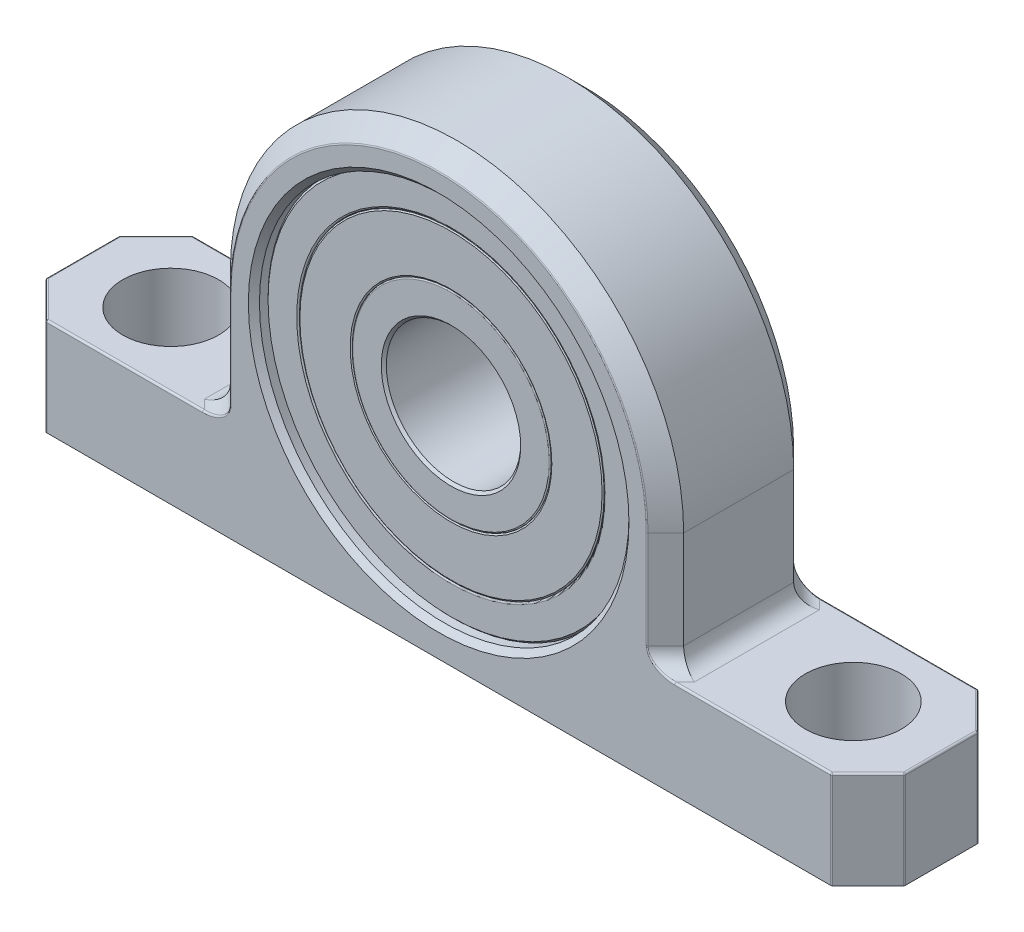
SolidWorks part; units mm, degrees
ref_plane "Front Plane" through (0, 0, 0) normal (0, 0, 1) x (1, 0, 0)
ref_plane "Top Plane" through (0, 0, 0) normal (0, 1, 0) x (1, 0, 0)
ref_plane "Right Plane" through (0, 0, 0) normal (1, 0, 0) x (0, 0, -1)
sketch "Sketch1" plane through (0, 0, 0) normal (0, 0, 1) x (1, 0, 0)
  line L0 (33.7344, 0) -> (33.7344, -17.272)
  line L1 (33.7344, -17.272) -> (63.8969, -17.272)
  line L2 (63.8969, -17.272) -> (63.8969, -31.75)
  line L3 (63.8969, -31.75) -> (-63.8969, -31.75)
  line L4 (-63.8969, -31.75) -> (-63.8969, -17.272)
  line L5 (-63.8969, -17.272) -> (-33.7344, -17.272)
  line L6 (-33.7344, -17.272) -> (-33.7344, 0)
  circle A0 centre (0, 0) radius 10
  arc A1 (33.7344, 0) -> (-33.7344, 0) centre (0, 0) ccw
  circle A2 centre (0, 0) radius 27.5
  point P12 (0, 27.5)
  point P13 (0, 10)
  dimension "ID" = 20
  dimension "Bearing OD" = 55
  dimension "Block OD" = 67.4688
  dimension "Collar Height" = 14.478
  dimension "Overall Length" = 127.7937
  dimension "Center Height" = 31.75
  dimension "Overall Height" = 65.4844
sketch "Sketch2" plane through (0, 0, 0) normal (0, 1, 0) x (1, 0, 0)
  line L0 (0, 10.9141) -> (0, -10.9141) construction
  line L1 (-50.8, 0) -> (50.8, 0) construction
  circle A0 centre (50.8, 0) radius 7.1437 construction
  circle A1 centre (-50.8, 0) radius 7.1437 construction
  dimension "Mounting Hole Diameter" = 14.2875
  dimension "Overall Width" = 21.8281
  dimension "Mounting Hole Center -to-Center" = 101.6
sketch "Sketch3" plane through (0, 0, 0) normal (0, 0, 1) x (1, 0, 0)
  line L0 (33.7344, 0) -> (33.7344, -17.272) construction
  line L1 (63.8969, -17.272) -> (63.8969, -31.75) construction
  line L2 (33.7344, -17.272) -> (63.8969, -17.272) construction
  line L3 (63.8969, -31.75) -> (-63.8969, -31.75) construction
  line L4 (-63.8969, -31.75) -> (-63.8969, -17.272) construction
  line L5 (-63.8969, -17.272) -> (-33.7344, -17.272) construction
  line L6 (-33.7344, -17.272) -> (-33.7344, 0) construction
  line L7 (33.7344, 0) -> (33.7344, -17.272)
  line L8 (63.8969, -17.272) -> (63.8969, -31.75)
  line L9 (33.7344, -17.272) -> (63.8969, -17.272)
  line L10 (63.8969, -31.75) -> (-63.8969, -31.75)
  line L11 (-63.8969, -31.75) -> (-63.8969, -17.272)
  line L12 (-63.8969, -17.272) -> (-33.7344, -17.272)
  line L13 (-33.7344, -17.272) -> (-33.7344, 0)
  arc A0 (33.7344, 0) -> (-33.7344, 0) centre (0, 0) ccw construction
  circle A1 centre (0, 0) radius 27.5 construction
  arc A2 (33.7344, 0) -> (-33.7344, 0) centre (0, 0) ccw
  circle A3 centre (0, 0) radius 27.5
extrude "Extrude1" add sketch "Sketch3" along normal up to vertex (10.9141 mm away) and the other way up to vertex (10.9141 mm away) up to point (0, 0, 10.9141) other way up to point (0, 0, -10.9141)
sketch "Sketch4" plane through (0, -17.272, 0) normal (0, 1, 0) x (1, 0, 0)
  line L0 (-63.8969, 10.9141) -> (-63.8969, 5.457)
  line L1 (-63.8969, -10.9141) -> (-63.8969, 10.9141) construction
  line L2 (-63.8969, 5.457) -> (-58.4398, 10.9141)
  line L3 (-33.7344, 10.9141) -> (-63.8969, 10.9141) construction
  line L4 (-58.4398, 10.9141) -> (-63.8969, 10.9141)
  line L5 (0, 0) -> (0, 10.9141) construction
  line L6 (0, 0) -> (-50.8, 0) construction
  line L7 (58.4398, 10.9141) -> (63.8969, 10.9141)
  line L8 (63.8969, 5.457) -> (58.4398, 10.9141)
  line L9 (63.8969, 10.9141) -> (63.8969, 5.457)
  line L10 (63.8969, -10.9141) -> (63.8969, -5.457)
  line L11 (63.8969, -5.457) -> (58.4398, -10.9141)
  line L12 (58.4398, -10.9141) -> (63.8969, -10.9141)
  line L13 (-58.4398, -10.9141) -> (-63.8969, -10.9141)
  line L14 (-63.8969, -5.457) -> (-58.4398, -10.9141)
  line L15 (-63.8969, -10.9141) -> (-63.8969, -5.457)
  circle A0 centre (-50.8, 0) radius 7.1437 construction
  circle A1 centre (50.8, 0) radius 7.1437 construction
  circle A2 centre (-50.8, 0) radius 7.1437
  circle A3 centre (50.8, 0) radius 7.1437
  dimension "D1" = 45
  dimension "D2" = 5.457
extrude "Cut-Extrude1" cut sketch "Sketch4" against normal through all
chamfer "Chamfer3" distance 2.7285 angle 45 6 edges at (-33.7344, -8.636, -10.9141) (0, 33.7344, -10.9141) (33.7344, -8.636, -10.9141) (-33.7344, -8.636, 10.9141) (0, 33.7344, 10.9141) (33.7344, -8.636, 10.9141)
fillet "Fillet6" radius 2.7285 6 edges at (33.7344, -17.272, 0) (32.3701, -17.272, -9.5498) (32.3701, -17.272, 9.5498) (-32.3701, -17.272, -9.5498) (-32.3701, -17.272, 9.5498) (-33.7344, -17.272, 0)
fillet "Fillet7" radius 0.2729 28 edges at (46.6522, -17.272, -10.9141) (32.136, -16.4728, -10.9141) (31.0059, -7.2717, -10.9141) (0, 31.0059, -10.9141) (-31.0059, -7.2717, -10.9141) (-32.136, -16.4728, -10.9141) (46.6522, -17.272, 10.9141) (32.136, -16.4728, 10.9141) (31.0059, -7.2717, 10.9141) (0, 31.0059, 10.9141) (-31.0059, -7.2717, 10.9141) (-32.136, -16.4728, 10.9141) (61.1684, -17.272, 8.1855) (63.8969, -17.272, 0) (61.1684, -17.272, -8.1855) (-46.6522, -17.272, -10.9141) (-61.1684, -17.272, -8.1855) (-63.8969, -17.272, 0) (-61.1684, -17.272, 8.1855) (-46.6522, -17.272, 10.9141) (-63.8969, -24.511, -5.457) (-58.4398, -24.511, -10.9141) (-63.8969, -24.511, 5.457) (-58.4398, -24.511, 10.9141) (58.4398, -24.511, -10.9141) (63.8969, -24.511, -5.457) (63.8969, -24.511, 5.457) (58.4398, -24.511, 10.9141)
chamfer "Chamfer4" distance 0.825 angle 45 2 edges at (27.5, 0, -10.9141) (27.5, 0, 10.9141)
sketch "Sketch5" plane through (0, 0, 0) normal (1, 0, 0) x (0, 0, -1)
  line L2 (9.0802, 27.5) -> (9.0802, 22.6875)
  line L4 (9.0802, 22.6875) -> (-9.0802, 22.6875)
  line L8 (-9.0802, 10) -> (9.0802, 10)
  line L9 (9.0802, 14.8125) -> (-9.0802, 14.8125)
  line L10 (-9.0802, 27.5) -> (9.0802, 27.5)
  line L12 (-9.0802, 14.8125) -> (-9.0802, 10)
  line L13 (-9.0802, 27.5) -> (-9.0802, 22.6875)
  line L17 (0, 27.5) -> (0, 33.7344) construction
  line L18 (0, 33.7344) -> (0, 0) construction
  line L24 (9.0802, 14.8125) -> (9.0802, 10)
  line L27 (8.1855, 33.7344) -> (-8.1855, 33.7344) construction
  dimension "D1" = 17.5
  dimension "D2" = 7.875
  dimension "D3" = 18.1603
  dimension "D4" = 18.1603
revolve "Revolve1" add sketch "Sketch5" angle 360 about L0
sketch "Sketch6" plane through (0, 0, 0) normal (1, 0, 0) x (0, 0, -1)
  line L9 (9.0802, 14.8125) -> (-9.0802, 14.8125) construction
  line L10 (0, 0) -> (0, 2.6695) construction
  line L19 (0, 0) -> (1.2184, 0) construction
  line L21 (-9.0802, 22.6875) -> (-6.8101, 22.6875)
  line L23 (-9.0802, 22.6875) -> (-9.0802, 14.8125)
  line L24 (-9.0802, 14.8125) -> (-6.8101, 14.8125)
  line L25 (-6.8101, 22.6875) -> (-6.8101, 14.8125)
  line L27 (9.0802, 22.6875) -> (6.8101, 22.6875)
  line L28 (9.0802, 22.6875) -> (9.0802, 14.8125)
  line L29 (9.0802, 14.8125) -> (6.8101, 14.8125)
  line L30 (6.8101, 22.6875) -> (6.8101, 14.8125)
  dimension "D1" = 2.27
revolve "Revolve2" add sketch "Sketch6" angle 360 about L19
chamfer "Chamfer5" distance 0.375 angle 45 2 edges at (-10, 0, 9.0802) (-10, 0, -9.0802)
fillet "Fillet8" radius 0.2 2 edges at (-14.8125, 0, -9.0802) (-14.8125, 0, 9.0802)
fillet "Fillet9" radius 0.275 2 edges at (-22.6875, 0, -9.0802) (-22.6875, 0, 9.0802)
chamfer "Chamfer6" distance 0.275 angle 45 2 edges at (-27.5, 0, -9.0802) (-27.5, 0, 9.0802)
chamfer "Chamfer7" distance 0.2 angle 30 2 edges at (22.6875, 0, 9.0802) (14.8125, 0, 9.0802)
chamfer "Chamfer8" distance 0.2 angle 30 2 edges at (22.6875, 0, -9.0802) (14.8125, 0, -9.0802)
equation "\"D2@Sketch4\" = \"Overall Width@Sketch2\" / 4"
equation "\"D1@Chamfer3\"=\"Overall Width@Sketch2\" / 8"
equation "\"D1@Fillet6\"=\"D1@Chamfer3\""
equation "\"D3@Sketch5\"=(\"Overall Width@Sketch2\"-2*\"D1@Chamfer4\")*.9"
equation "\"D1@Chamfer5\"=\"ID@Sketch1\"*.01875"
equation "\"D1@Fillet8\"=\"ID@Sketch1\"*.01"
equation "\"D1@Fillet9\"=\"Bearing OD@Sketch1\"*.005"
equation "\"D1@Chamfer6\"=\"Bearing OD@Sketch1\"*.005"
equation "\"D1@Chamfer4\"=\"Bearing OD@Sketch1\"*.015"
equation "\"D1@Fillet7\"=\"Overall Width@Sketch2\"*.0125"
equation "\"D2@Sketch5\"=(\"Bearing OD@Sketch1\"-\"ID@Sketch1\")/2*.45"
equation "\"D1@Sketch6\"=\"D3@Sketch5\"/8"
equation "\"D1@Chamfer7\"=\"ID@Sketch1\"*.01"
equation "\"D1@Chamfer8\"=\"ID@Sketch1\"*.01"
